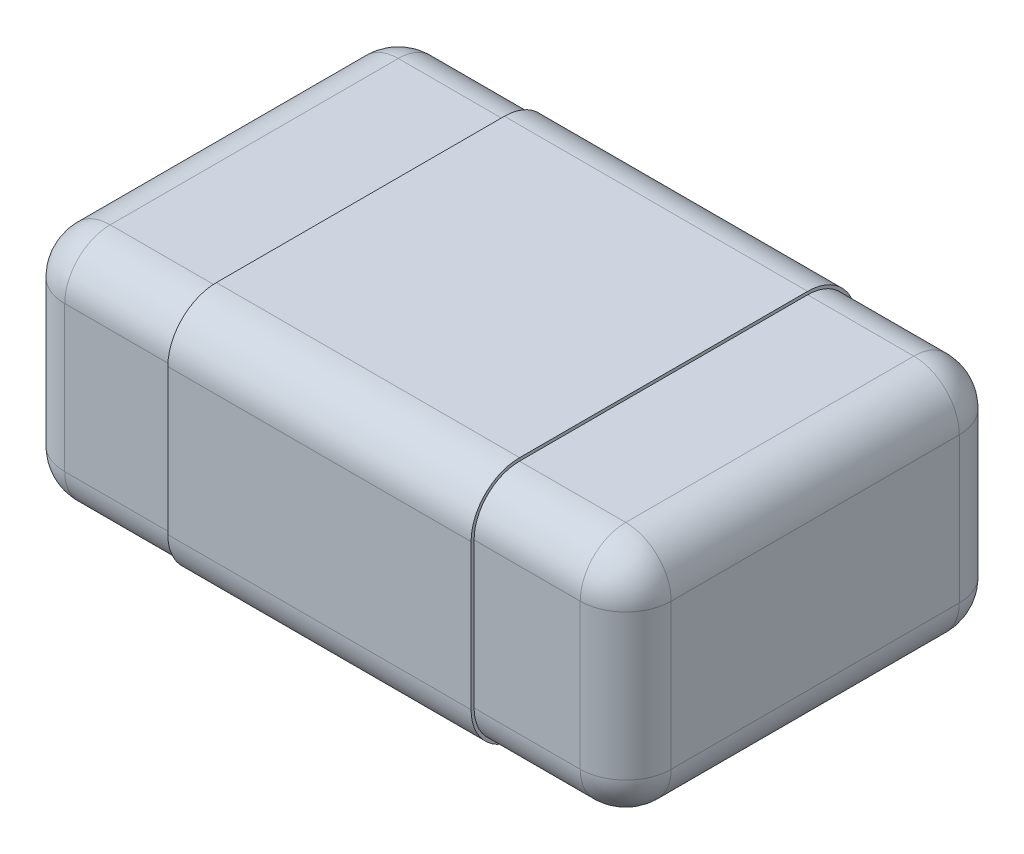
SolidWorks part; units mm, degrees
material "Aço inoxidável fundido"
ref_plane "Plano frontal" through (0, 0, 0) normal (0, 0, 1) x (1, 0, 0)
ref_plane "Plano superior" through (0, 0, 0) normal (0, 1, 0) x (1, 0, 0)
ref_plane "Plano direito" through (0, 0, 0) normal (1, 0, 0) x (0, 0, -1)
sketch "Esboço1" plane through (0, 0, 0) normal (0, 1, 0) x (1, 0, 0)
  line L0 (-1, -0.625) -> (1, -0.625)
  line L1 (1, -0.625) -> (1, 0.625)
  line L2 (1, 0.625) -> (-1, 0.625)
  line L3 (-1, 0.625) -> (-1, -0.625)
extrude "Ressalto-extrusão1" add sketch "Esboço1" against normal blind 0.78
fillet "Filete1" radius 0.15 12 edges at (0, -0.78, -0.625) (-1, -0.39, -0.625) (1, -0.39, -0.625) (0, 0, -0.625) (-1, -0.78, 0) (1, -0.78, 0) (0, -0.78, 0.625) (-1, 0, 0) (1, 0, 0) (-1, -0.39, 0.625) (1, -0.39, 0.625) (0, 0, 0.625)
sketch "Esboço4" plane through (0, 0, 0) normal (1, 0, 0) x (0, 0, -1)
  line L0 (0.625, -0.63) -> (0.625, -0.15) construction
  line L1 (0.625, -0.63) -> (0.625, -0.15)
  line L2 (0.475, -0.78) -> (-0.475, -0.78) construction
  line L3 (0.475, -0.78) -> (-0.475, -0.78)
  line L4 (0.475, 0) -> (-0.475, 0) construction
  line L5 (-0.625, -0.15) -> (-0.625, -0.63) construction
  line L6 (0.475, 0) -> (-0.475, 0)
  line L7 (-0.625, -0.15) -> (-0.625, -0.63)
  line L8 (0.635, -0.63) -> (0.635, -0.15)
  line L9 (0.475, 0.01) -> (-0.475, 0.01)
  line L10 (-0.635, -0.15) -> (-0.635, -0.63)
  line L11 (0.475, -0.79) -> (-0.475, -0.79)
  arc A5 (0.475, -0.78) -> (0.625, -0.63) centre (0.475, -0.63) ccw construction
  arc A6 (0.475, -0.78) -> (0.625, -0.63) centre (0.475, -0.63) ccw
  arc A7 (-0.475, 0) -> (-0.625, -0.15) centre (-0.475, -0.15) ccw construction
  arc A8 (-0.625, -0.63) -> (-0.475, -0.78) centre (-0.475, -0.63) ccw construction
  arc A9 (-0.475, 0) -> (-0.625, -0.15) centre (-0.475, -0.15) ccw
  arc A10 (-0.625, -0.63) -> (-0.475, -0.78) centre (-0.475, -0.63) ccw
  arc A11 (0.625, -0.15) -> (0.475, 0) centre (0.475, -0.15) ccw construction
  arc A12 (0.625, -0.15) -> (0.475, 0) centre (0.475, -0.15) ccw
  arc A13 (0.635, -0.15) -> (0.475, 0.01) centre (0.475, -0.15) ccw
  arc A14 (-0.475, 0.01) -> (-0.635, -0.15) centre (-0.475, -0.15) ccw
  arc A15 (-0.635, -0.63) -> (-0.475, -0.79) centre (-0.475, -0.63) ccw
  arc A16 (0.475, -0.79) -> (0.635, -0.63) centre (0.475, -0.63) ccw
  dimension "D1" = 0.01
extrude "Ressalto-extrusão4" add sketch "Esboço4" along normal blind 0.5 and the other way blind 0.5
sketch "Esboço2" plane through (0, -0.79, 0) normal (0, -1, 0) x (0, 0, 1)
  line L1 (-0.475, 0.5) -> (0.475, 0.5) construction
  line L2 (-0.475, -0.5) -> (0.475, -0.5) construction
  line L7 (0.2404, -0.5) -> (0.2404, 0.5) construction
  text T0 "<b>122</b>" font "Tahoma" height 0.5
extrude "Ressalto-extrusão5" add sketch "Esboço2" along normal blind 0.02
